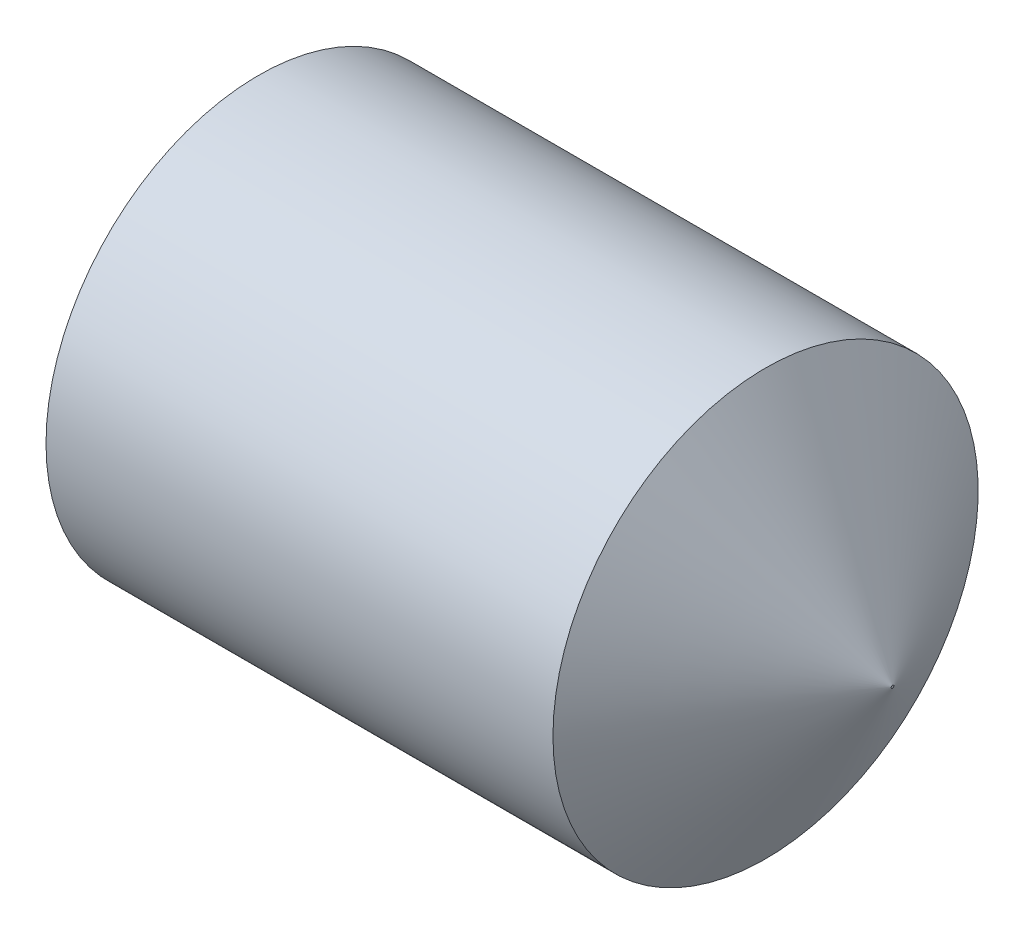
SolidWorks part; units mm, degrees
revolve "BaseBody" add sketch "BodySke" angle 360 about L5
sketch "BodySke" plane through (0, 0, 0) normal (0, 0, 1) x (1, 0, 0)
  line L0 (0, 0) -> (0, 0.601)
  line L1 (0, 0.601) -> (0.1149, 0.8)
  line L2 (0.1149, 0.8) -> (2.0223, 0.8)
  line L3 (2.5, 0) -> (2.5, 0.005)
  line L4 (2.5, 0) -> (0, 0)
  line L5 (-12.7, 0) -> (88.9, 0) construction
  line L6 (2.5, 0.005) -> (2.0223, 0.8)
  line L7 (0.35, 15.875) -> (0.35, -3.175) construction
  line L8 (0, -0.601) -> (0.1149, -0.8) construction
  line L9 (2.5, -0.005) -> (2.0223, -0.8) construction
  dimension "Diameter" = 1.6
  dimension "Drive_ch_ang" = 60
  dimension "Minor_dia" = 1.202
  dimension "Advance" = 0.35
  dimension "Tip_dia" = 0.01
  dimension "Cone_ang" = 118
cosmetic thread "ThreadCosmetic" [suppressed] parameters "Thread_minor"=1.202
ref_plane "Plane1" through (0, 0, 0) normal (0, 0, 1) x (1, 0, 0)
ref_plane "Plane2" through (0, 0, 0) normal (0, 1, 0) x (1, 0, 0)
ref_plane "Plane3" through (0, 0, 0) normal (1, 0, 0) x (0, 0, -1)
sketch "Sketch2" plane through (0, 0, 0) normal (-1, 0, 0) x (0, 0, 1)
  line L0 (0.2021, 0.35) -> (-0.2021, 0.35)
  line L1 (-0.2021, 0.35) -> (-0.4041, 0)
  line L2 (0.2021, 0.35) -> (0.4041, 0)
  line L3 (0.2021, -0.35) -> (0.4041, 0)
  line L4 (0.2021, -0.35) -> (-0.2021, -0.35)
  line L5 (-0.2021, -0.35) -> (-0.4041, 0)
  dimension "Hex_size" = 0.7
  dimension "D2" = 0.35
  dimension "D3" = 0.35
extrude "Hex" cut sketch "Sketch2" against normal blind 1
sketch "Sketch4" plane through (0, 4.7709, -0.5249) normal (-1, 0, 0) x (0, 0, 1)
  line L0 (0.5249, -4.7709) -> (0.9694, -4.7709)
  line L1 (0.5249, -4.7709) -> (5.545, 0.2492) construction
  line L2 (0.5249, -4.7709) -> (0.5249, -4.3264)
  line L3 (0.8397, -4.6718) -> (0.928, -4.5835)
  line L4 (0.624, -4.4561) -> (0.7123, -4.3678)
  arc A0 (0.8397, -4.6718) -> (0.624, -4.4561) centre (0.5249, -4.7709) ccw
  arc A1 (0.9694, -4.7709) -> (0.928, -4.5835) centre (0.5249, -4.7709) ccw
  arc A2 (0.5249, -4.3264) -> (0.7123, -4.3678) centre (0.5249, -4.7709) cw
  circle A3 centre (0.5249, -4.7709) radius 0.33 construction
  circle A4 centre (0.5249, -4.7709) radius 0.4445 construction
  dimension "Spline_n_dim" = 0.66
  dimension "Spline_m_dim" = 0.889
  dimension "D1" = 45
  dimension "Spline_a_dim" = 90
  dimension "Spline_p_dim" = 0.305
  dimension "D3" = 0.1525
extrude "Spline6" [suppressed] cut sketch "Sketch4" against normal blind 0.7
pattern_circular "CirPattern1" [suppressed] count 4 every 90 about axis through (-12.7, 0, 0) along (1, 0, 0)
sketch "Sketch5" plane through (0, 1.4735, 6.925) normal (-1, 0, 0) x (0, 0, 1)
  line L0 (-6.925, -1.4735) -> (-6.4805, -1.4735)
  line L1 (-6.925, -1.4735) -> (-1.9049, 3.5466) construction
  line L2 (-6.925, -1.4735) -> (-6.925, -1.029)
  line L3 (-6.5839, -1.348) -> (-6.522, -1.2861)
  line L4 (-6.7995, -1.1323) -> (-6.7376, -1.0704)
  line L5 (-6.7995, -1.1323) -> (-6.5839, -1.348)
  arc A1 (-6.4805, -1.4735) -> (-6.522, -1.2861) centre (-6.925, -1.4735) ccw
  arc A2 (-6.925, -1.029) -> (-6.7376, -1.0704) centre (-6.925, -1.4735) cw
  circle A3 centre (-6.925, -1.4735) radius 0.33 construction
  circle A4 centre (-6.925, -1.4735) radius 0.4445 construction
  dimension "Spline_n_dim" = 0.66
  dimension "Spline_m_dim" = 0.889
  dimension "D1" = 45
  dimension "Spline_a_dim" = 90
  dimension "Spline_p_dim" = 0.305
  dimension "D3" = 0.1525
extrude "Spline4" [suppressed] cut sketch "Sketch5" against normal blind 0.7
pattern_circular "CirPattern2" [suppressed] count 4 every 90 about axis through (-12.7, 0, 0) along (1, 0, 0)
sketch "ThdSchSke" plane through (0, 0, 0) normal (0, 0, 1) x (1, 0, 0)
  line L0 (0.1149, -0.601) -> (-0.0244, -0.8)
  line L1 (0.1149, -0.601) -> (0.2542, -0.8)
  line L2 (0.2542, -0.8) -> (0.2542, -1)
  line L3 (-3.175, 0) -> (5.1513, 0) construction
  line L4 (0.1149, 0.8) -> (0.1149, -0.8) construction
  line L5 (0.2542, -1) -> (-0.0244, -1)
  line L6 (-0.0244, -1) -> (-0.0244, -0.8)
  dimension "Thread_minor" = 1.202
  dimension "Diameter" = 1.6
revolve "ThreadSchematic" [suppressed] cut sketch "ThdSchSke" angle 360 about L3
pattern_linear "ThdSchPat" [suppressed]
equation "\"D2@Sketch2\" = \"Hex_size@Sketch2\" / 2"
equation "\"D3@Sketch2\" = \"Hex_size@Sketch2\" / 2"
equation "\"Thread_minor@ThreadCosmetic\" = \"Minor_dia@BodySke\""
equation "\"D1@Sketch4\" = \"Spline_a_dim@Sketch4\" / 2"
equation "\"D3@Sketch4\" = \"Spline_p_dim@Sketch4\" / 2"
equation "\"D2@CirPattern1\" = \"Spline_a_dim@Sketch4\""
equation "\"Num_teeth@CirPattern1\" = 360 / \"D2@CirPattern1\""
equation "\"Spline_a_dim@Sketch5\" = 90"
equation "\"Spline_p_dim@Sketch5\" = \"Spline_p_dim@Sketch4\""
equation "\"Spline_m_dim@Sketch5\" = \"Spline_m_dim@Sketch4\""
equation "\"Spline_n_dim@Sketch5\" = \"Spline_n_dim@Sketch4\""
equation "\"D1@Sketch5\" = \"Spline_a_dim@Sketch5\" / 2"
equation "\"D3@Sketch5\" = \"Spline_p_dim@Sketch5\" / 2"
equation "\"Key_eng@Spline4\" = \"Key_eng@Spline6\""
equation "\"Thread_minor@ThdSchSke\" = \"Thread_minor@ThreadCosmetic\""
equation "\"Diameter@ThdSchSke\" = \"Diameter@BodySke\""
equation "\"Overcut@ThdSchSke\" = \"Diameter@BodySke\" * 1.25"
equation "\"Num_threads@ThdSchPat\" = int( (\"Length@BodySke\" - ( ( ( \"Diameter@BodySke\" - \"Minor_dia@BodySke\" ) * 0.5 ) / tan( \"Drive_ch_ang@BodySke\" * 0.017453292 ) ) - ( ( \"Diameter@BodySke\" * 0.5 ) / tan( \"Cone_ang@BodySke\" * 0.008726646 ) ) ) / \"Advance@BodySke\" + 0.999 )  + 1"
equation "\"Num_threads@ThdSchPat\" = int( (\"Length@BodySke\" - ( ( ( \"Diameter@BodySke\" - \"Minor_dia@BodySke\" ) * 0.5 ) / tan( \"Drive_ch_ang@BodySke\" * 0.017453292 ) ) - ( (( \"Diameter@BodySke\" - \"Tip_dia@BodySke\") * 0.5 ) / tan( \"Cone_ang@BodySke\" * 0.008726646 ) ) ) / \"Advance@BodySke\" + 0.999 )  + 1"
equation "\"Advance@ThdSchPat\" = (\"Length@BodySke\" - ( ( ( \"Diameter@BodySke\" - \"Minor_dia@BodySke\" ) * 0.5 ) / tan( \"Drive_ch_ang@BodySke\" * 0.017453292 ) ) - ( ( \"Diameter@BodySke\" * 0.5 ) / tan( \"Cone_ang@BodySke\" * 0.008726646 ) ) ) /  (\"Num_threads@ThdSchPat\" - 1) 'relax it"
equation "\"Advance@ThdSchPat\" = (\"Length@BodySke\" - ( ( ( \"Diameter@BodySke\" - \"Minor_dia@BodySke\" ) * 0.5 ) / tan( \"Drive_ch_ang@BodySke\" * 0.017453292 ) ) - ( ( (\"Diameter@BodySke\" - \"Tip_dia@BodySke\") * 0.5 ) / tan( \"Cone_ang@BodySke\" * 0.008726646 ) ) ) /  (\"Num_threads@ThdSchPat\" - 1) 'relax it"
equation "' \"Num_threads@ThdSchPat\" = \"Num_threads@ThdSchPat\" - sgn( \"Num_threads@ThdSchPat\" - 1) '---chamfered tips only---"
